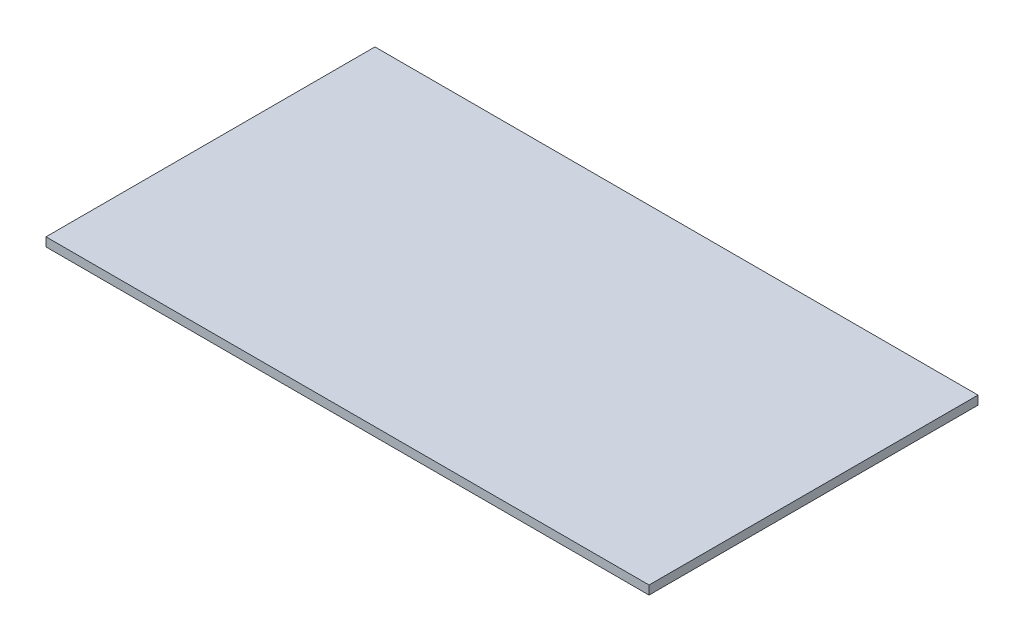
SolidWorks part; units mm, degrees
ref_plane "Front Plane" through (0, 0, 0) normal (0, 0, 1) x (1, 0, 0)
ref_plane "Top Plane" through (0, 0, 0) normal (0, 1, 0) x (1, 0, 0)
ref_plane "Right Plane" through (0, 0, 0) normal (1, 0, 0) x (0, 0, -1)
sketch "Sketch1" plane through (0, 0, 0) normal (0, 1, 0) x (1, 0, 0)
  line L1 (-275, -150) -> (275, -150)
  line L2 (-275, -150) -> (-275, 150)
  line L3 (-275, 150) -> (275, 150)
  line L4 (275, -150) -> (275, 150)
  line L5 (-275, -150) -> (275, 150) construction
  line L6 (-275, 150) -> (275, -150) construction
  point P0 (0, 0)
  dimension "D1" = 550
  dimension "D2" = 300
extrude "Boss-Extrude1" add sketch "Sketch1" along normal blind 8
